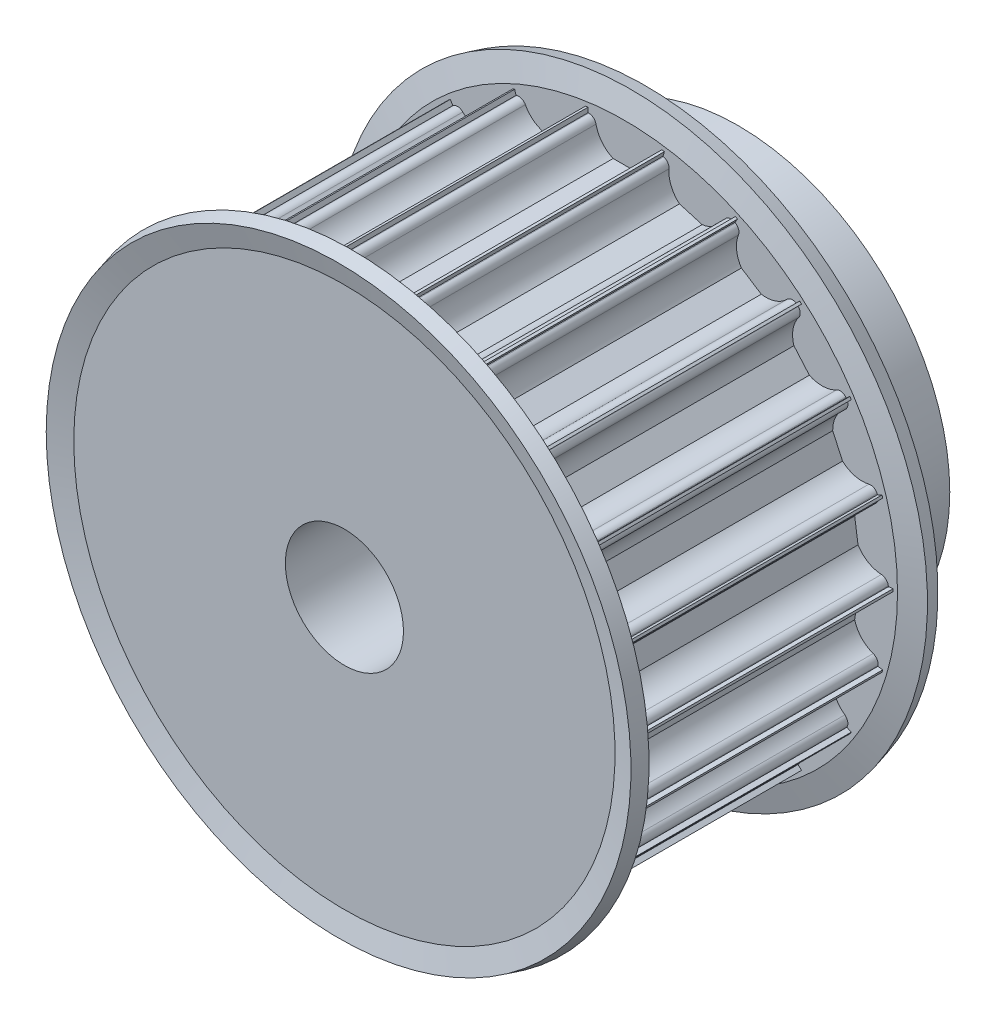
SolidWorks part; units mm, degrees
ref_plane "Front Plane" through (0, 0, 0) normal (0, 0, 1) x (1, 0, 0)
ref_plane "Top Plane" through (0, 0, 0) normal (0, 1, 0) x (1, 0, 0)
ref_plane "Right Plane" through (0, 0, 0) normal (1, 0, 0) x (0, 0, -1)
sketch "Sketch1" plane through (0, 0, 0) normal (1, 0, 0) x (0, 0, -1)
  line L0 (0, 0) -> (25.0004, 0) construction
  line L1 (0, 6) -> (0, 27.25)
  line L2 (0, 27.25) -> (30, 27.25)
  line L3 (30, 27.25) -> (30, 21.5)
  line L4 (30, 21.5) -> (40, 21.5)
  line L5 (40, 21.5) -> (40, 6)
  line L6 (0, 6) -> (40, 6)
  dimension "D1" = 6
  dimension "D2" = 27.25
  dimension "D3" = 30
  dimension "D4" = 10
  dimension "D5" = 15.5
revolve "Revolve1" add sketch "Sketch1" angle 360 about L0
sketch "Sketch2" plane through (0, 0, 0) normal (0, 0, 1) x (1, 0, 0)
  line L0 (-3.6742, 26.5) -> (-3.75, 26.5)
  line L1 (-3.75, 26.5) -> (-3.75, 28.5)
  line L2 (-3.75, 28.5) -> (3.75, 28.5)
  line L3 (3.75, 28.5) -> (3.75, 26.5)
  line L4 (3.6742, 26.5) -> (3.75, 26.5)
  line L5 (-1.199, 23.75) -> (1.199, 23.75)
  arc A0 (2.9394, 25.9) -> (1.199, 23.75) centre (0, 26.5) cw
  arc A1 (3.6742, 26.5) -> (2.9394, 25.9) centre (3.6742, 25.75) ccw
  arc A2 (-2.9394, 25.9) -> (-3.6742, 26.5) centre (-3.6742, 25.75) ccw
  arc A3 (-1.199, 23.75) -> (-2.9394, 25.9) centre (0, 26.5) cw
  point P9 (3, 26.5)
  point P12 (-3, 26.5)
  dimension "D1" = 3
  dimension "D5" = 0.75
  dimension "D2" = 26.5
  dimension "D3" = 7.5
  dimension "D4" = 2
  dimension "D6" = 2.75
extrude "Cut-Extrude1" cut sketch "Sketch2" against normal up to next (30 mm away)
pattern_circular "CirPattern2" count 22 over 360 about axis through (0, 0, 0) along (0, 0, 1) of "Cut-Extrude1"
sketch "Sketch3" plane through (0, 0, 0) normal (1, 0, 0) x (0, 0, -1)
  line L0 (15, 26.9539) -> (15, -26.9539) construction
  line L1 (30, 26.9539) -> (0, 26.9539) construction
  line L2 (0, -26.9539) -> (30, -26.9539) construction
  line L3 (30, 21.5) -> (30, 27.4925)
  line L4 (30, 27.4925) -> (30.592, 29.7018)
  line L5 (30.592, 29.7018) -> (29.1431, 30.09)
  line L6 (29.1431, 30.09) -> (28.5, 27.69)
  line L7 (28.5, 27.69) -> (28.5, 21.5)
  line L8 (28.5, 21.5) -> (30, 21.5)
  line L9 (0, 27.4925) -> (-0.592, 29.7018)
  line L10 (-0.592, 29.7018) -> (0.8569, 30.09)
  line L11 (0.8569, 30.09) -> (1.5, 27.69)
  line L12 (1.5, 27.69) -> (1.5, 21.5)
  line L13 (1.5, 21.5) -> (0, 21.5)
  line L14 (0, 21.5) -> (0, 27.4925)
  line L15 (0, 0) -> (-18.4442, 0) construction
  dimension "D1" = 15
  dimension "D2" = 6.19
  dimension "D3" = 2.4
  dimension "D4" = 1.5
revolve "Revolve2" add sketch "Sketch3" angle 360 about L15
